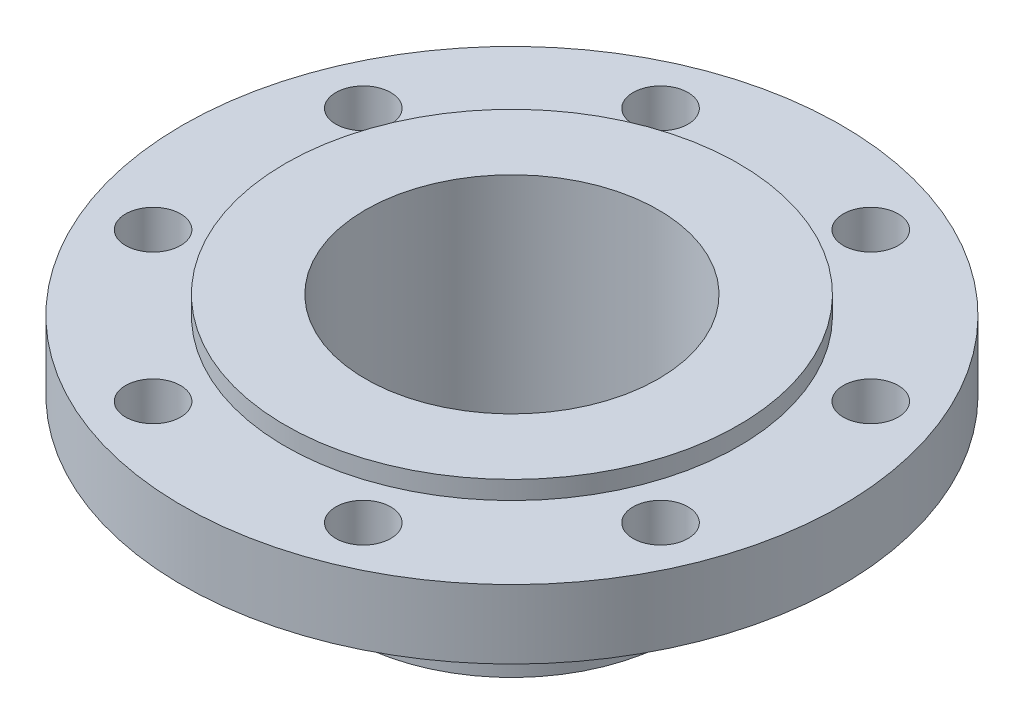
SolidWorks part; units mm, degrees
ref_plane "Front Plane" through (0, 0, 0) normal (0, 0, 1) x (1, 0, 0)
ref_plane "Top Plane" through (0, 0, 0) normal (0, 1, 0) x (1, 0, 0)
ref_plane "Right Plane" through (0, 0, 0) normal (1, 0, 0) x (0, 0, -1)
sketch "Main" plane through (0, 0, 0) normal (0, 0, 1) x (1, 0, 0)
  line L0 (0, 0) -> (-78.613, 0)
  line L1 (0, 0) -> (0, -74.676) construction
  line L2 (-78.613, 0) -> (-78.613, -6.35)
  line L3 (-78.613, -6.35) -> (-114.3, -6.35)
  line L4 (-114.3, -6.35) -> (-114.3, -30.226)
  line L5 (-114.3, -30.226) -> (-67.437, -30.226)
  line L6 (-67.437, -30.226) -> (-57.15, -66.3787)
  line L7 (-57.15, -66.3787) -> (-57.15, -74.676)
  line L8 (-57.15, -74.676) -> (0, -74.676)
  line L9 (0, 0) -> (0, -74.676)
  dimension "HubLength" = 74.676
  dimension "RaisedFaceDiameter" = 157.226
  dimension "OutsideDiameter" = 228.6
  dimension "FlangeThickness" = 23.876
  dimension "PipeDiameter" = 114.3
  dimension "RaisedFaceDepth" = 6.35
  dimension "HubDiameter" = 134.874
  dimension "Offset" = 8.2973
revolve "Revolve1" add sketch "Main" angle 360 about L1
sketch "BoreSketch" plane through (0, 0, 0) normal (0, 1, 0) x (1, 0, 0)
  circle A0 centre (0, 0) radius 50.8
  dimension "Bore" = 101.6
extrude "Bore" cut sketch "BoreSketch" against normal through all
sketch "Sketch3" plane through (0, -6.35, 0) normal (0, 1, 0) x (1, 0, 0)
  line L0 (0, 0) -> (0, 95.25) construction
  line L1 (0, 0) -> (-36.4506, 87.9995) construction
  circle A0 centre (0, 0) radius 95.25 construction
  circle A1 centre (-36.4506, 87.9995) radius 9.525
  dimension "BoltHoleCircle" = 190.5
  dimension "BoltDiameter" = 19.05
  dimension "HoleLocation" = 22.5
extrude "Bolt Hole" cut sketch "Sketch3" against normal through all contours A1
pattern_circular "Bolt Pattern" count 8 over 360 about axis through (0, 0, 0) along (0, 1, 0) of "Bolt Hole"
